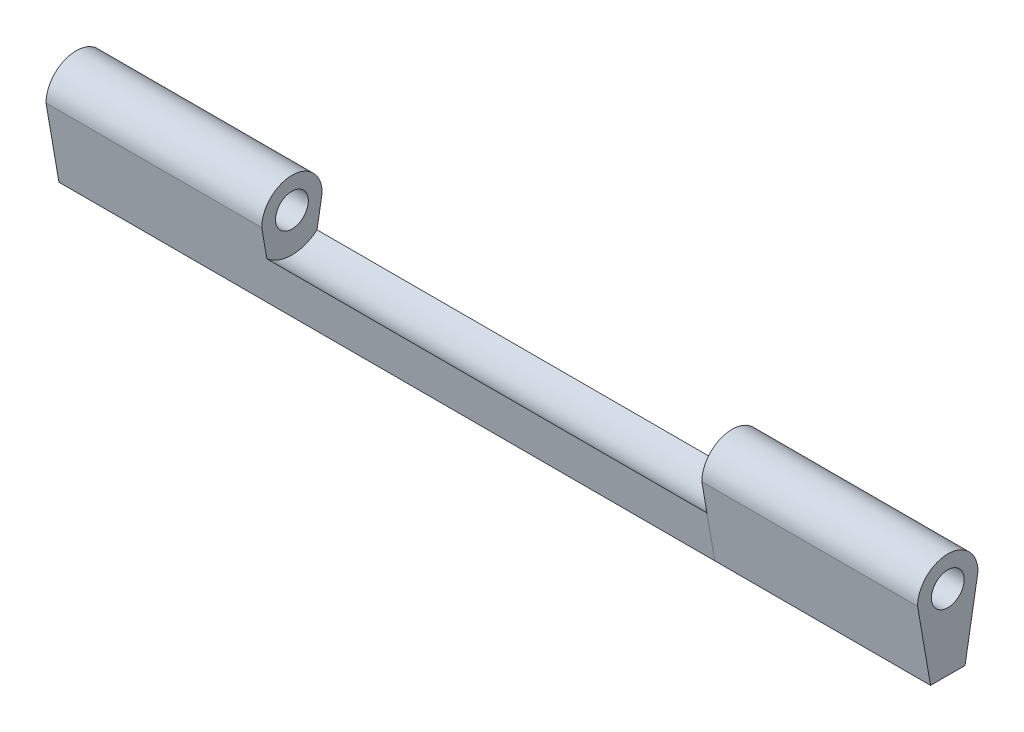
SolidWorks part; units mm, degrees
ref_plane "Front Plane" through (0, 0, 0) normal (0, 0, 1) x (1, 0, 0)
ref_plane "Top Plane" through (0, 0, 0) normal (0, 1, 0) x (1, 0, 0)
ref_plane "Right Plane" through (0, 0, 0) normal (1, 0, 0) x (0, 0, -1)
sketch "Sketch1" plane through (0, 0, 0) normal (1, 0, 0) x (0, 0, -1)
  line L0 (2, -8.7) -> (3.5, 0)
  line L5 (-2, -8.7) -> (2, -8.7)
  line L7 (-3.5, 0) -> (-2, -8.7)
  circle A0 centre (0, 0) radius 1.9
  arc A1 (3.5, 0) -> (-3.5, 0) centre (0, 0) ccw
  circle A3 centre (0, 0) radius 3.5 construction
  point P5 (0, -8.7)
  point P16 (2.51, 0)
  dimension "D1" = 3.8
  dimension "D3" = 8.7
  dimension "D4" = 4
  dimension "D2" = 1.6
extrude "Boss-Extrude1" add sketch "Sketch1" along normal blind 25
sketch "Sketch2" plane through (25, 0, 0) normal (1, 0, 0) x (0, 0, -1)
  line L0 (-2, -8.7) -> (2, -8.7)
  line L1 (2, -8.7) -> (2.9079, -3.4343)
  line L2 (2, -8.7) -> (3.5, 0) construction
  line L3 (-2.9079, -3.4343) -> (-2, -8.7)
  line L4 (-3.5, 0) -> (-2, -8.7) construction
  arc A0 (-1.9, 0) -> (1.9, 0) centre (0, 0) ccw construction
  circle A1 centre (0, 0) radius 1.9 construction
  arc A2 (-2.9079, -3.4343) -> (2.9079, -3.4343) centre (0, 0) ccw
  arc A4 (-4.5, 0) -> (4.5, 0) centre (0, 0) ccw construction
  dimension "D1" = 4.5
extrude "Boss-Extrude2" add sketch "Sketch2" along normal blind 51
sketch "Sketch3" plane through (76, 0, 0) normal (1, 0, 0) x (0, 0, -1)
  line L0 (-3.5, 0) -> (-2, -8.7)
  line L1 (-2, -8.7) -> (2, -8.7)
  line L2 (2, -8.7) -> (3.5, 0)
  circle A0 centre (0, 0) radius 1.51
  arc A1 (-3.5, 0) -> (3.5, 0) centre (0, 0) cw
  arc A2 (3.5, 0) -> (-3.5, 0) centre (0, 0) ccw construction
extrude "Boss-Extrude3" add sketch "Sketch3" along normal blind 25
sketch "Sketch7" plane through (101, 0, 0) normal (1, 0, 0) x (0, 0, -1)
  circle A0 centre (0, 0) radius 1.9
  dimension "D1" = 3.8
extrude "Cut-Extrude4" cut sketch "Sketch7" against normal through all
